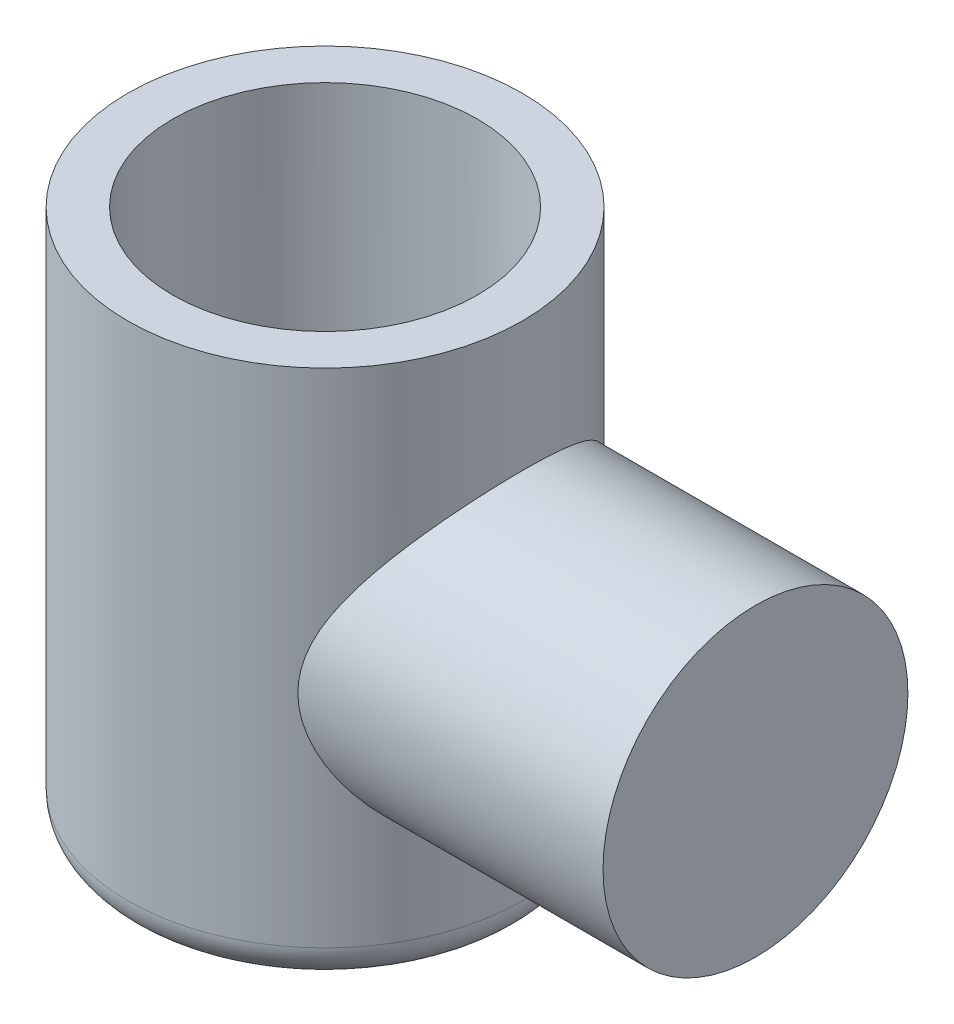
SolidWorks part; units mm, degrees
ref_plane "Front Plane" through (0, 0, 0) normal (0, 0, 1) x (1, 0, 0)
ref_plane "Top Plane" through (0, 0, 0) normal (0, 1, 0) x (1, 0, 0)
ref_plane "Right Plane" through (0, 0, 0) normal (1, 0, 0) x (0, 0, -1)
sketch "Sketch1" plane through (0, 0, 0) normal (0, 1, 0) x (1, 0, 0)
  circle A0 centre (0, 0) radius 55
  dimension "D1" = 110
extrude "Boss-Extrude1" add sketch "Sketch1" along normal blind 150
sketch "Sketch3" plane through (0, 150, 0) normal (0, 1, 0) x (1, 0, 0)
  circle A0 centre (0, 0) radius 42.5
  dimension "D1" = 85
fillet "Fillet1" radius 10 1 edges at (0, 0, 55)
extrude "Cut-Extrude2" cut sketch "Sketch3" against normal blind 85 contours A0
sketch "Sketch5" plane through (0, 0, 0) normal (1, 0, 0) x (0, 0, -1)
sketch "Sketch13" plane through (0, 0, 0) normal (1, 0, 0) x (0, 0, -1)
  circle A0 centre (0, 71.3599) radius 42.5
  dimension "D1" = 85
extrude "Boss-Extrude3" add sketch "Sketch13" along normal blind 120
